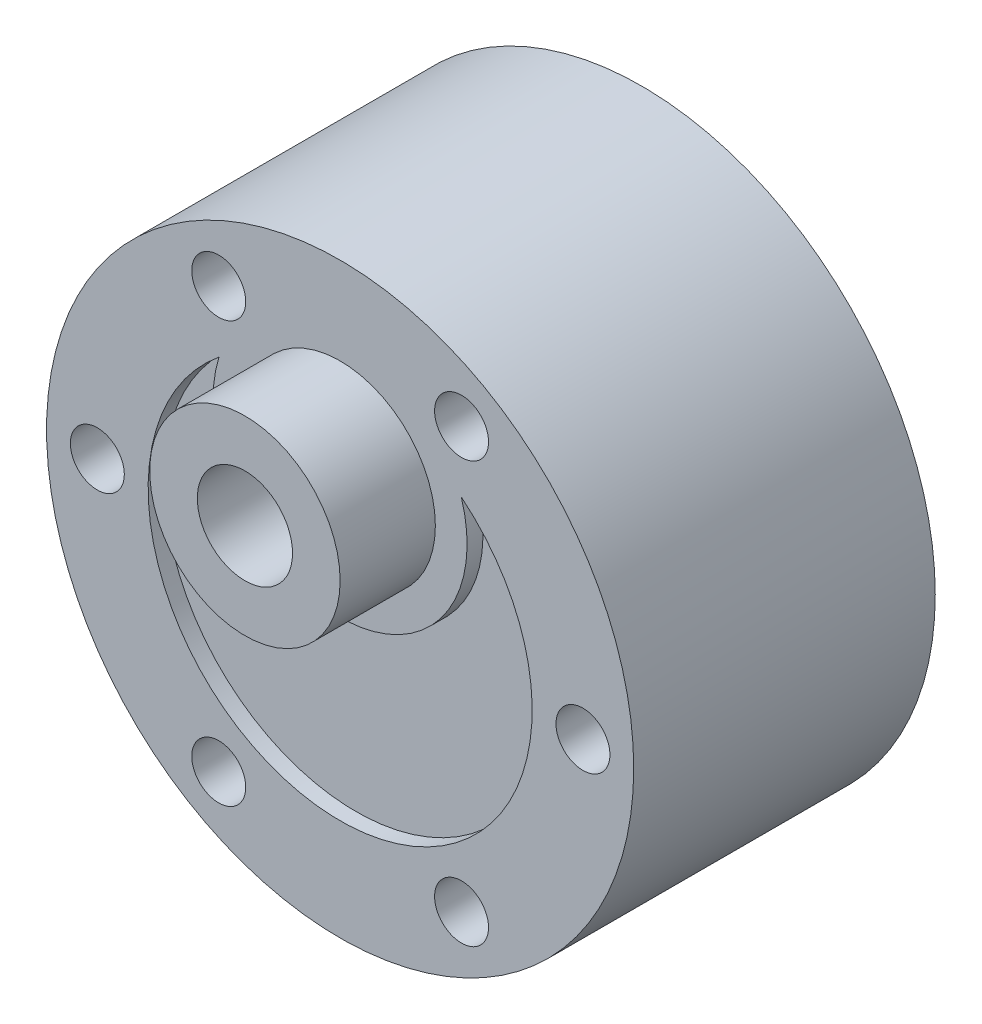
SolidWorks part; units mm, degrees
ref_plane "Front Plane" through (0, 0, 0) normal (0, 0, 1) x (1, 0, 0)
ref_plane "Top Plane" through (0, 0, 0) normal (0, 1, 0) x (1, 0, 0)
ref_plane "Right Plane" through (0, 0, 0) normal (1, 0, 0) x (0, 0, -1)
sketch "Sketch1" plane through (0, 0, 0) normal (0, 0, 1) x (1, 0, 0)
  circle A0 centre (0, 0) radius 18.5
  dimension "D1" = 37
extrude "Boss-Extrude1" add sketch "Sketch1" along normal blind 19
sketch "Sketch4" plane through (0, 0, 19) normal (0, 0, 1) x (1, 0, 0)
  circle A0 centre (0, 7) radius 6
  circle A1 centre (0, 0) radius 18.5 construction
  dimension "D1" = 12
  dimension "D2" = 7
extrude "Boss-Extrude4" add sketch "Sketch4" along normal blind 6
sketch "Sketch8" plane through (0, 0, 19) normal (0, 0, 1) x (1, 0, 0)
  circle A0 centre (0, 0) radius 18.5 construction
  arc A1 (7.6358, 9.3864) -> (-7.6358, 9.3864) centre (0, 0) cw
  arc A3 (-7.6358, 9.3864) -> (7.6358, 9.3864) centre (0, 7) ccw
  dimension "D1" = 8
  dimension "D2" = 12.1
  dimension "D3" = 6.4
  dimension "D4" = 7
extrude "Cut-Extrude2" cut sketch "Sketch8" against normal blind 1
hole_wizard "Taladro de margen para M31" positions "Sketch9" profile "Sketch10" hole size "M3" standard "Ansi Metric"
sketch "Sketch9" plane through (0, 0, 19) normal (0, 0, 1) x (1, 0, 0)
  line L0 (0, 0) -> (0, -7.0626) construction
  line L2 (7.65, -13.2502) -> (0, 0) construction
  line L3 (-7.65, -13.2502) -> (0, 0) construction
  line L5 (-15.3, 0) -> (0, 0) construction
  line L6 (0, 0) -> (-7.65, 13.2502) construction
  line L8 (0, 0) -> (15.3, 0) construction
  line L9 (0, 0) -> (7.65, 13.2502) construction
  circle A0 centre (0, 0) radius 15.3
  point P0 (7.65, -13.2502)
  point P23 (-7.65, -13.2502)
  point P25 (-15.3, 0)
  point P27 (-7.65, 13.2502)
  point P32 (15.3, 0)
  point P60 (7.65, 13.2502)
  dimension "D1" = 15.3
  dimension "D2" = 30
  dimension "D3" = 30
  dimension "D4" = 60
  dimension "D5" = 60
  dimension "D6" = 60
  dimension "D7" = 60
sketch "Sketch10" plane through (7.65, -13.2502, 19) normal (1, 0, 0) x (0, -1, 0)
  line L0 (0, 0) -> (0, 7.0215)
  line L1 (0, 7.0215) -> (1.7, 6)
  line L2 (1.7, 6) -> (1.7, 0)
  line L3 (-22.6366, 0) -> (-12.2502, 0) construction
  line L5 (1.7, 0) -> (0, 0)
  line L10 (0, 7.0215) -> (-1.7, 6) construction
  line L11 (0, -6.35) -> (0, 107.95) construction
  dimension "Hole Dia." = 3.4
  dimension "Hole Depth" = 6
  dimension "Drill Angle" = 118
sketch "Croquis1" plane through (0, 0, 0) normal (0, 0, -1) x (-1, 0, 0)
  circle A0 centre (0, 0) radius 18
extrude "Cortar-Extruir2" cut sketch "Croquis1" against normal blind 12
sketch "Croquis2" plane through (0, 0, 25) normal (0, 0, 1) x (1, 0, 0)
  line L0 (0, 0) -> (0, 7) construction
  line L1 (0, 0) -> (7.65, 13.2502) construction
  line L2 (0, 0) -> (-7.65, 13.2145) construction
  line L3 (0, 0) -> (-15.3, -0.0357) construction
  line L4 (0, 0) -> (15.3, -0.0357) construction
  circle A0 centre (0, 7) radius 3
  circle A1 centre (7.65, 13.2502) radius 1.7 construction
  circle A2 centre (7.65, 13.2502) radius 1.7
  circle A4 centre (-7.65, 13.2502) radius 1.7 construction
  circle A5 centre (-7.65, 13.2502) radius 0.0357 construction
  circle A6 centre (-15.3, 0) radius 0.0357 construction
  circle A8 centre (15.3, 0) radius 0.0357 construction
  dimension "D1" = 15.3
extrude "Cortar-Extruir3" cut sketch "Croquis2" against normal up to next
sketch "Croquis3" plane through (0, 0, 0) normal (0, 0, -1) x (-1, 0, 0)
  circle A0 centre (0, 0) radius 18
extrude "Saliente-Extruir1" add sketch "Croquis3" against normal blind 0.5
sketch "Sketch11" plane through (0, 0, 0) normal (0, 0, -1) x (-1, 0, 0)
  circle A0 centre (0, 0) radius 2
extrude "Cut-Extrude3" cut sketch "Sketch11" against normal blind 10
sketch "Sketch12" plane through (0, 0, 0) normal (0, 0, -1) x (-1, 0, 0)
  line L0 (0, 0) -> (0, -15) construction
  line L1 (-6.25, -14.25) -> (6.25, -14.25)
  line L2 (-6.25, -14.25) -> (-6.25, -15.75)
  line L3 (-6.25, -15.75) -> (6.25, -15.75)
  line L4 (6.25, -14.25) -> (6.25, -15.75)
  line L5 (-6.25, -14.25) -> (6.25, -15.75) construction
  line L6 (-6.25, -15.75) -> (6.25, -14.25) construction
  point P0 (0, -15)
  dimension "D1" = 1.5
  dimension "D2" = 12.5
  dimension "D3" = 15
extrude "Cut-Extrude4" cut sketch "Sketch12" against normal blind 0.15
sketch "Sketch13" plane through (0, 0, 0) normal (0, 0, -1) x (-1, 0, 0)
  circle A1 centre (0, 0) radius 6
  dimension "D2" = 12
extrude "Cut-Extrude5" cut sketch "Sketch13" against normal blind 10
sketch "Sketch14" plane through (0, 0, 12) normal (0, 0, -1) x (-1, 0, 0)
  line L0 (0, 7) -> (0, -5.15) construction
  circle A0 centre (0, -5.15) radius 2
  circle A1 centre (0, -5.15) radius 2.25
  dimension "D1" = 4
  dimension "D3" = 4.5
  dimension "D2" = 12.15
extrude "Boss-Extrude5" add sketch "Sketch14" along normal blind 1
